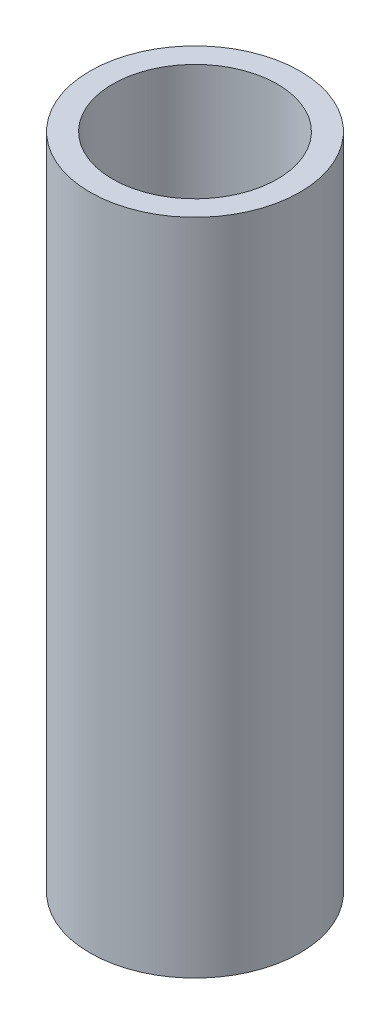
SolidWorks part; units mm, degrees
material "PVC Rigid"
ref_plane "Front Plane" through (0, 0, 0) normal (0, 0, 1) x (1, 0, 0)
ref_plane "Top Plane" through (0, 0, 0) normal (0, 1, 0) x (1, 0, 0)
ref_plane "Right Plane" through (0, 0, 0) normal (1, 0, 0) x (0, 0, -1)
sketch "Sketch1" plane through (0, 0, 0) normal (0, 1, 0) x (1, 0, 0)
  circle A0 centre (0, 0) radius 24.2824
  circle A1 centre (0, 0) radius 19.05
  dimension "D1" = 38.1
  dimension "D2" = 48.5648
extrude "Boss-Extrude1" add sketch "Sketch1" along normal mid plane 152.4
